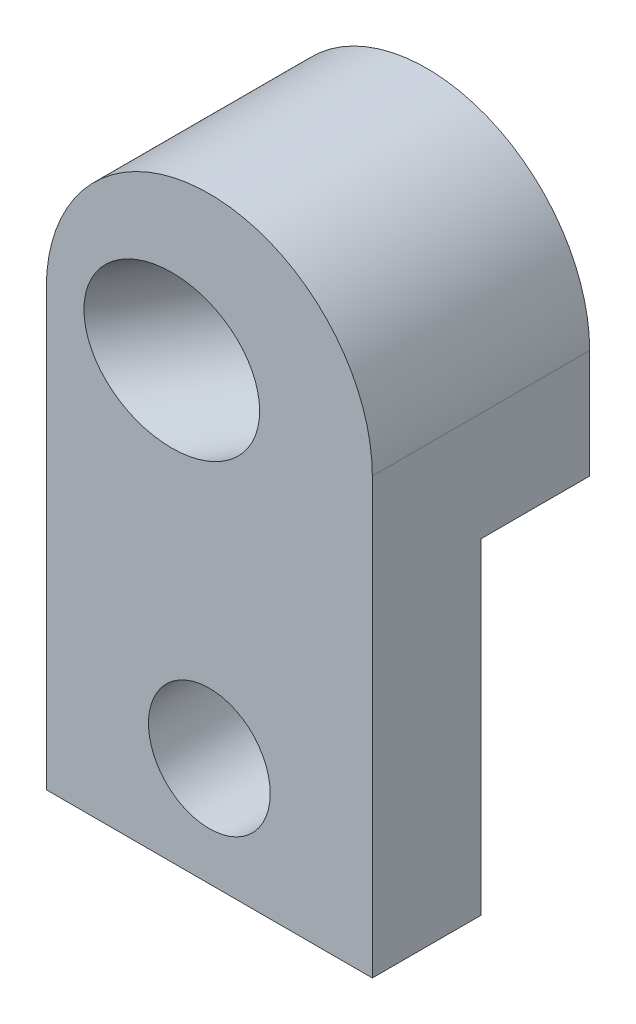
SolidWorks part; units mm, degrees
ref_plane "Front Plane" through (0, 0, 0) normal (0, 0, 1) x (1, 0, 0)
ref_plane "Top Plane" through (0, 0, 0) normal (0, 1, 0) x (1, 0, 0)
ref_plane "Right Plane" through (0, 0, 0) normal (1, 0, 0) x (0, 0, -1)
sketch "Sketch2" plane through (0, 0, 0) normal (0, 0, 1) x (1, 0, 0)
  line L0 (0, 0) -> (15, 0)
  line L1 (15, 0) -> (15, 20)
  line L2 (0, 20) -> (0, 0)
  line L3 (0, 5) -> (7.5, 5) construction
  line L4 (7.5, 5) -> (7.5, 0) construction
  line L5 (7.5, 5) -> (15, 5) construction
  arc A0 (15, 20) -> (0, 20) centre (7.5, 20) ccw
  circle A1 centre (7.5, 5) radius 2.8
  dimension "D1" = 5.6
  dimension "D3" = 20
  dimension "D2" = 15
  dimension "D4" = 5
extrude "Boss-Extrude1" add sketch "Sketch2" along normal blind 5
sketch "Sketch3" plane through (0, 0, 0) normal (0, 0, -1) x (-1, 0, 0)
  line L0 (-15, 20) -> (-15, 15)
  line L1 (-15, 0) -> (-15, 20) construction
  line L2 (-15, 15) -> (0, 15)
  line L3 (0, 20) -> (0, 0) construction
  line L4 (0, 15) -> (0, 20)
  arc A0 (0, 20) -> (-15, 20) centre (-7.5, 20) ccw
  dimension "D1" = 5
extrude "Boss-Extrude2" add sketch "Sketch3" along normal blind 5
ref_plane "Plane1" through (-2.1651, 0, 3.75) normal (-0.5, 0, 0.866) x (0, -1, 0)
sketch "Sketch4" plane through (-2.1651, 0, 3.75) normal (-0.5, 0, 0.866) x (0, -1, 0)
  line L0 (-20, 2.5) -> (0, 2.5) construction
  circle A0 centre (-20, 7.5) radius 3.5
  dimension "D1" = 7
  dimension "D2" = 5
extrude "Cut-Extrude1" cut sketch "Sketch4" against normal blind 10
